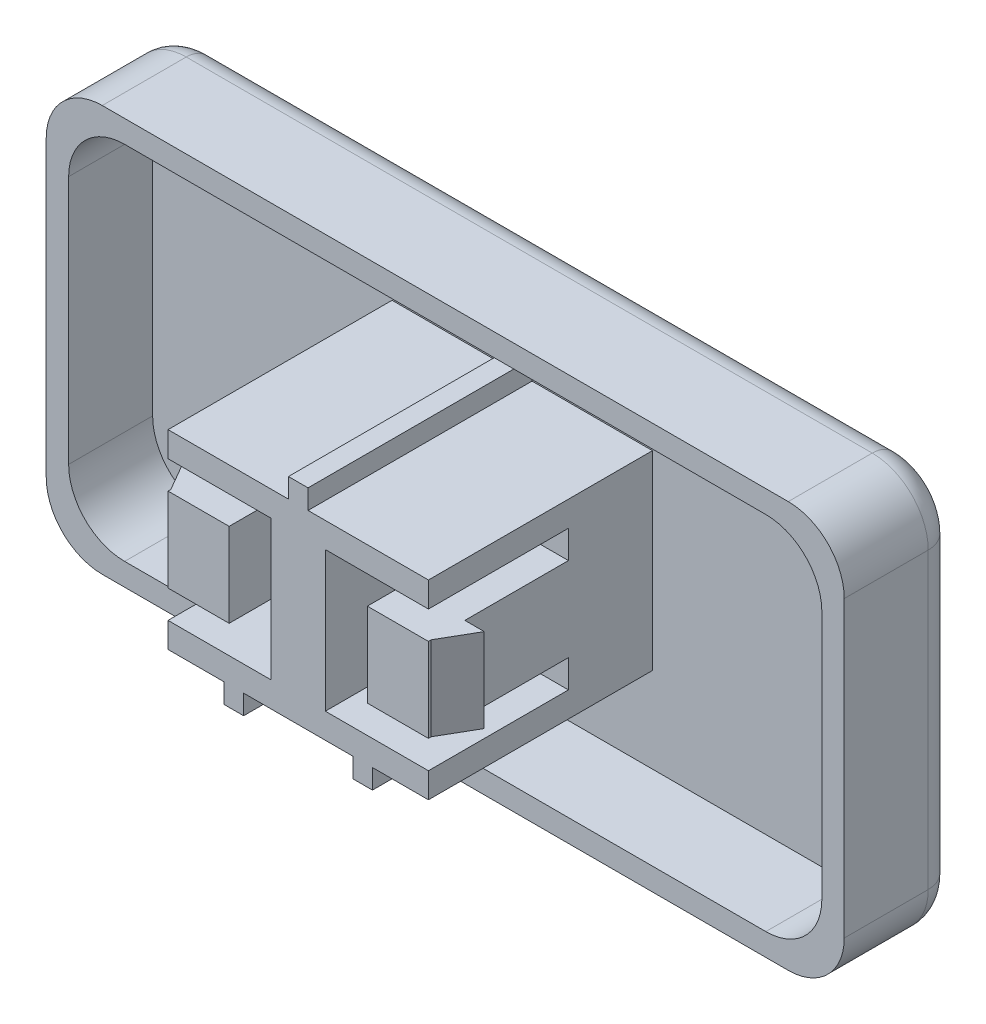
SolidWorks part; units mm, degrees
ref_plane "Alzado" through (0, 0, 0) normal (0, 0, 1) x (1, 0, 0)
ref_plane "Planta" through (0, 0, 0) normal (0, 1, 0) x (1, 0, 0)
ref_plane "Vista lateral" through (0, 0, 0) normal (1, 0, 0) x (0, 0, -1)
sketch "Croquis1" plane through (0, 0, 0) normal (0, 0, 1) x (1, 0, 0)
  line L1 (-48.5532, 12.5111) -> (-20.0532, 12.5111)
  line L2 (-48.5532, 12.5111) -> (-48.5532, -1.9889)
  line L3 (-48.5532, -1.9889) -> (-20.0532, -1.9889)
  line L4 (-20.0532, 12.5111) -> (-20.0532, -1.9889)
  dimension "D1" = 28.5
  dimension "D2" = 14.5
extrude "Saliente-Extruir1" add sketch "Croquis1" along normal blind 1
sketch "Croquis2" plane through (0, 0, 1) normal (0, 0, 1) x (1, 0, 0)
  line L8 (-47.7532, 11.7111) -> (-47.7532, -1.1889)
  line L9 (-47.7532, -1.1889) -> (-20.8532, -1.1889)
  line L10 (-20.8532, -1.1889) -> (-20.8532, 11.7111)
  line L11 (-20.8532, 11.7111) -> (-47.7532, 11.7111)
  line L12 (-47.7532, 11.7111) -> (-47.7532, -1.1889)
  line L13 (-47.7532, -1.1889) -> (-20.8532, -1.1889)
  line L14 (-20.8532, -1.1889) -> (-20.8532, 11.7111)
  line L15 (-20.8532, 11.7111) -> (-47.7532, 11.7111)
  line L20 (-48.5532, 12.5111) -> (-48.5532, -1.9889)
  line L21 (-48.5532, -1.9889) -> (-20.0532, -1.9889)
  line L22 (-20.0532, -1.9889) -> (-20.0532, 12.5111)
  line L23 (-20.0532, 12.5111) -> (-48.5532, 12.5111)
  line L24 (-48.5532, 12.5111) -> (-48.5532, -1.9889)
  line L25 (-48.5532, -1.9889) -> (-20.0532, -1.9889)
  line L26 (-20.0532, -1.9889) -> (-20.0532, 12.5111)
  line L27 (-20.0532, 12.5111) -> (-48.5532, 12.5111)
  dimension "D1" = 0.8
  dimension "D2" = 0
extrude "Saliente-Extruir2" add sketch "Croquis2" along normal blind 3
sketch "Croquis3" plane through (0, 0, 1) normal (0, 0, 1) x (1, 0, 0)
  line L0 (-47.7532, 11.7111) -> (-47.7532, -1.1889) construction
  line L1 (-34.5532, 1.8611) -> (-34.5532, -1.2889) construction
  line L2 (-39.2032, 8.6611) -> (-34.9032, 8.6611)
  line L3 (-39.2032, 8.6611) -> (-39.2032, 1.8611)
  line L4 (-39.2032, 1.8611) -> (-37.2032, 1.8611)
  line L5 (-29.9032, 8.6611) -> (-29.9032, 1.8611)
  line L6 (-39.2032, 8.6611) -> (-29.9032, 1.8611) construction
  line L7 (-39.2032, 1.8611) -> (-29.9032, 8.6611) construction
  line L9 (-34.9032, 8.6611) -> (-34.9032, 9.3611)
  line L10 (-34.9032, 9.3611) -> (-34.2032, 9.3611)
  line L11 (-34.2032, 8.6611) -> (-34.2032, 9.3611)
  line L13 (-37.2032, 1.8611) -> (-37.2032, 1.1611)
  line L14 (-37.2032, 1.1611) -> (-36.5032, 1.1611)
  line L15 (-36.5032, 1.8611) -> (-36.5032, 1.1611)
  line L17 (-34.2032, 8.6611) -> (-29.9032, 8.6611)
  line L18 (-36.5032, 1.8611) -> (-32.6032, 1.8611)
  line L19 (-32.6032, 1.8611) -> (-32.6032, 1.1611)
  line L20 (-31.9032, 1.1611) -> (-32.6032, 1.1611)
  line L21 (-31.9032, 1.8611) -> (-31.9032, 1.1611)
  line L22 (-31.9032, 1.8611) -> (-29.9032, 1.8611)
  line L23 (-20.8532, -1.1889) -> (-20.8532, 11.7111) construction
  point P4 (-34.5532, 5.2611)
  point P14 (-34.5532, 9.3611)
  point P28 (-20.8532, 5.2611)
  dimension "D1" = 9.3
  dimension "D2" = 6.8
  dimension "D3" = 0.7
  dimension "D4" = 0.7
  dimension "D5" = 0.7
  dimension "D6" = 0.7
  dimension "D7" = 2
  dimension "D8" = 13.2
extrude "Saliente-Extruir3" add sketch "Croquis3" along normal blind 8
sketch "Croquis4" plane through (0, 0, 9) normal (0, 0, 1) x (1, 0, 0)
  line L0 (-39.2032, 6.7611) -> (-37.0212, 6.7611)
  line L1 (-39.2032, 8.6611) -> (-39.2032, 1.8611) construction
  line L2 (-37.0212, 6.7611) -> (-37.0212, 5.2611)
  line L3 (-39.2032, 5.2611) -> (-37.0212, 5.2611) construction
  line L4 (-39.2032, 7.7611) -> (-35.5212, 7.7611)
  line L5 (-35.5212, 7.7611) -> (-35.5212, 5.2611)
  line L6 (-39.2032, 7.7611) -> (-39.2032, 6.7611)
  line L7 (-39.2032, 2.7611) -> (-39.2032, 3.7611)
  line L8 (-35.5212, 2.7611) -> (-35.5212, 5.2611)
  line L9 (-39.2032, 2.7611) -> (-35.5212, 2.7611)
  line L10 (-37.0212, 3.7611) -> (-37.0212, 5.2611)
  line L11 (-39.2032, 3.7611) -> (-37.0212, 3.7611)
  line L12 (-34.5532, 9.3611) -> (-34.5532, 1.8611) construction
  line L13 (-34.2032, 9.3611) -> (-34.9032, 9.3611) construction
  line L14 (-36.5032, 1.8611) -> (-32.6032, 1.8611) construction
  line L15 (-29.9032, 5.2611) -> (-32.0853, 5.2611) construction
  line L16 (-29.9032, 3.7611) -> (-32.0853, 3.7611)
  line L17 (-32.0853, 3.7611) -> (-32.0853, 5.2611)
  line L18 (-29.9032, 2.7611) -> (-33.5853, 2.7611)
  line L19 (-33.5853, 2.7611) -> (-33.5853, 5.2611)
  line L20 (-29.9032, 2.7611) -> (-29.9032, 3.7611)
  line L21 (-29.9032, 7.7611) -> (-29.9032, 6.7611)
  line L22 (-33.5853, 7.7611) -> (-33.5853, 5.2611)
  line L23 (-29.9032, 7.7611) -> (-33.5853, 7.7611)
  line L24 (-32.0853, 6.7611) -> (-32.0853, 5.2611)
  line L25 (-29.9032, 6.7611) -> (-32.0853, 6.7611)
  point P4 (-39.2032, 5.2611)
  dimension "D1" = 1.5
  dimension "D2" = 1.5
  dimension "D3" = 1
extrude "Cortar-Extruir1" cut sketch "Croquis4" against normal blind 5
sketch "Croquis5" plane through (0, 3.7611, 0) normal (0, -1, 0) x (1, 0, 0)
  line L0 (-39.2032, 8.9) -> (-39.8961, 7.7)
  line L1 (-39.8961, 7.7) -> (-39.2032, 7.7)
  line L2 (-39.2032, 4) -> (-39.2032, 9) construction
  line L3 (-39.2032, 7.7) -> (-39.2032, 8.9)
  line L4 (-37.0212, 9) -> (-32.0853, 9) construction
  line L5 (-34.5532, 9) -> (-34.5532, 4.8665) construction
  line L6 (-29.9032, 7.7) -> (-29.9032, 8.9)
  line L7 (-29.2104, 7.7) -> (-29.9032, 7.7)
  line L8 (-29.9032, 8.9) -> (-29.2104, 7.7)
  dimension "D1" = 30
  dimension "D2" = 1.2
  dimension "D3" = 0.1
extrude "Saliente-Extruir4" add sketch "Croquis5" against normal up to surface (3 mm away) up to face at (-38.1122, 6.7611, 6.5)
fillet "Redondeo1" radius 2 8 edges at (-47.7532, -1.1889, 2.5) (-20.8532, -1.1889, 2.5) (-20.0532, 12.5111, 2) (-20.0532, -1.9889, 2) (-20.8532, 11.7111, 2.5) (-48.5532, 12.5111, 2) (-48.5532, -1.9889, 2) (-47.7532, 11.7111, 2.5)
fillet "Redondeo2" radius 1 8 edges at (-47.9675, -1.4032, 0) (-48.5532, 5.2611, 0) (-47.9675, 11.9253, 0) (-34.3032, 12.5111, 0) (-20.639, 11.9253, 0) (-20.0532, 5.2611, 0) (-20.639, -1.4032, 0) (-34.3032, -1.9889, 0)
